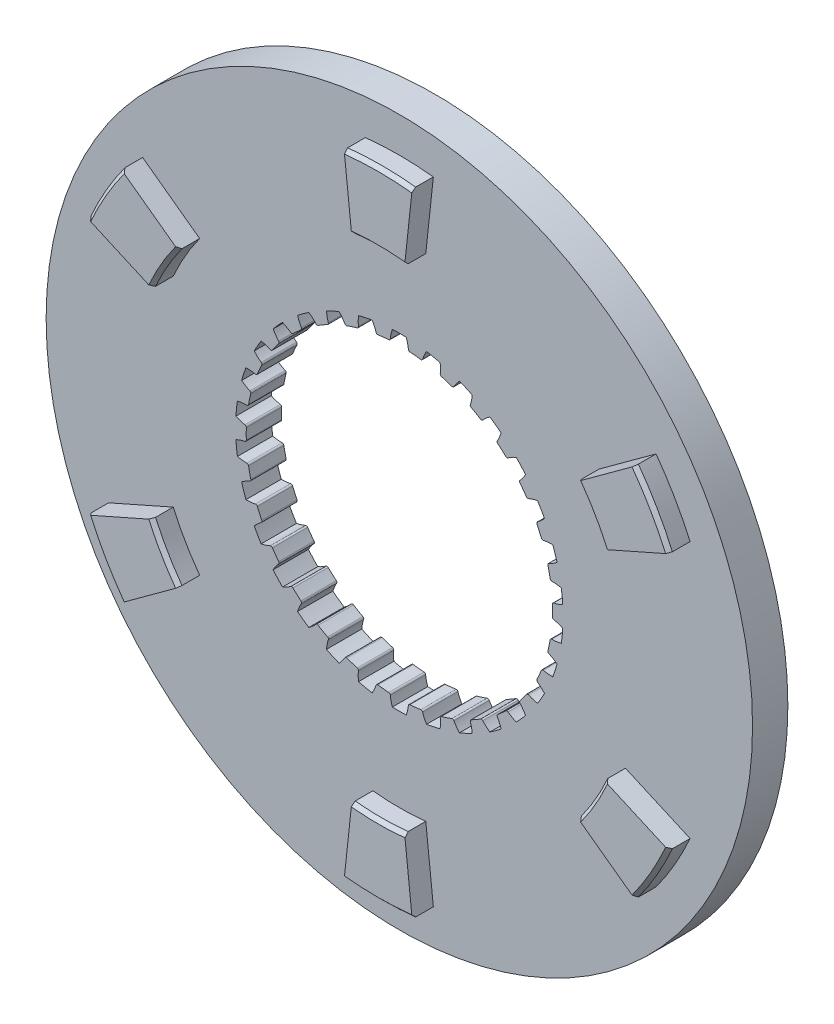
SolidWorks part; units mm, degrees
material "1.6587 (18CrNiMo7-6)"
ref_plane "Front Plane" through (0, 0, 0) normal (0, 0, 1) x (1, 0, 0)
ref_plane "Top Plane" through (0, 0, 0) normal (0, 1, 0) x (1, 0, 0)
ref_plane "Right Plane" through (0, 0, 0) normal (1, 0, 0) x (0, 0, -1)
sketch "Sketch1" plane through (0, 0, 0) normal (0, 0, 1) x (1, 0, 0)
  circle A1 centre (0, 0) radius 100
  dimension "D2" = 200
extrude "Boss-Extrude1" add sketch "Sketch1" along normal blind 10
sketch "Sketch2" plane through (0, 0, 10) normal (0, 0, 1) x (1, 0, 0)
  line L0 (0, 0) -> (10.2384, 95.1441)
  line L1 (0, 0) -> (-10.21, 94.8799)
  line L2 (0, 0) -> (0, 132.9785) construction
  line L3 (0, 0) -> (87.5164, 38.7053)
  line L4 (0, 0) -> (77.0634, 56.2821)
  line L5 (0, 0) -> (77.278, -56.4388)
  line L6 (0, 0) -> (87.2734, -38.5978)
  line L7 (0, 0) -> (-10.2384, -95.1441)
  line L8 (0, 0) -> (10.21, -94.8799)
  line L9 (0, 0) -> (-87.5164, -38.7053)
  line L10 (0, 0) -> (-77.0634, -56.2821)
  line L11 (0, 0) -> (-77.278, 56.4388)
  line L12 (0, 0) -> (-87.2734, 38.5978)
  circle A0 centre (0, 0) radius 70
  circle A1 centre (0, 0) radius 90
  point P19 (0, 0)
  dimension "D1" = 140
  dimension "D2" = 180
  dimension "D3" = 6
  dimension "D4" = 12.284
extrude "Boss-Extrude2" add sketch "Sketch2" along normal blind 6 contours L2 A0 L0 A1 | A0 L2 A1 L1 | L11 A1 L12 A0 | L9 A1 L10 A0 | L7 A1 L8 A0 | L5 A1 L6 A0 | L3 A1 L4 A0
chamfer "Chamfer1" distance 1 12 edges at (-77.9423, -45, 16) (-60.6218, -35, 16) (0, -70, 16) (0, -90, 16) (60.6218, -35, 16) (77.9423, -45, 16) (77.9423, 45, 16) (60.6218, 35, 16) (0, 70, 16) (0, 90, 16) (-77.9423, 45, 16) (-60.6218, 35, 16)
sketch "Sketch3" plane through (0, 0, 10) normal (0, 0, 1) x (1, 0, 0)
  line L0 (0, 0) -> (2.5692, 43.2738) construction
  line L1 (-9.3575, 42.328) -> (-12.2626, 41.5795) construction
  line L2 (0, 0) -> (-0.4299, 43.3479) construction
  line L3 (-0.4299, 43.3479) -> (2.5699, 43.3776) construction
  line L4 (0, 0) -> (-3.427, 43.2143) construction
  line L5 (-3.427, 43.2143) -> (2.5543, 43.6887) construction
  line L6 (0, 0) -> (-6.4076, 42.8738) construction
  line L7 (-6.4076, 42.8738) -> (2.4936, 44.2041) construction
  line L8 (0, 0) -> (-9.3575, 42.328) construction
  line L9 (-9.3575, 42.328) -> (2.3596, 44.9183) construction
  line L10 (2.5692, 43.2738) -> (-0.4299, 43.3479) construction
  line L11 (-0.4299, 43.3479) -> (-3.427, 43.2143) construction
  line L12 (-3.427, 43.2143) -> (-6.4076, 42.8738) construction
  line L13 (-6.4076, 42.8738) -> (-9.3575, 42.328) construction
  line L14 (0, 0) -> (-12.2626, 41.5795) construction
  line L15 (-12.2626, 41.5795) -> (2.1247, 45.8226) construction
  line L16 (0, 0) -> (-15.109, 40.6318) construction
  line L17 (-15.109, 40.6318) -> (1.7623, 46.9054) construction
  line L18 (-12.2626, 41.5795) -> (-15.109, 40.6318) construction
  line L19 (0, 0) -> (2.3551, 44.9383) construction
  line L20 (0, 0) -> (0, 54.7803) construction
  circle A0 centre (0, 0) radius 43.35
  circle A1 centre (0, 0) radius 45 construction
  circle A2 centre (0, 0) radius 46.35
  spline S0 degree 3 poles (2.5692, 43.2738) (2.5727, 43.4122) (2.544, 43.9656) (2.3322, 45.1974) (2.0036, 46.2564) (1.7623, 46.9054) knots 0 0 0 0 0.111137 0.444343 1 1 1 1
  spline S1 degree 3 poles (-2.5692, 43.2738) (-2.5727, 43.4122) (-2.544, 43.9656) (-2.3322, 45.1974) (-2.0036, 46.2564) (-1.7623, 46.9054) knots 0 0 0 0 0.111137 0.444343 1 1 1 1
  dimension "D1" = 86.7
  dimension "D2" = 90
  dimension "D3" = 92.7
  dimension "D4" = 3
  dimension "D5" = 3
  dimension "D6" = 6
  dimension "D7" = 9
  dimension "D8" = 12
  dimension "D9" = 15
  dimension "D10" = 18
  dimension "D11" = 3
extrude "Cut-Extrude2" cut sketch "Sketch3" against normal through all contours S1 A0 S0 A2
sketch "Sketch4" plane through (0, 0, 10) normal (0, 0, 1) x (1, 0, 0)
  circle A0 centre (0, 0) radius 43.35
  dimension "D1" = 86.7
extrude "Cut-Extrude3" cut sketch "Sketch4" against normal through all
fillet "Fillet2" radius 0.48 2 edges at (2.5692, 43.2738, 5) (-2.5692, 43.2738, 5)
pattern_circular "CirPattern3" count 30 over 360 about axis through (0, 0, 0) along (0, 0, 1) of "Cut-Extrude2", "Fillet2"
ref_plane "Plane1" through (0, 0, 5) normal (0, 0, 1) x (1, 0, 0)
mirror "Mirror1" about plane through (0, 0, 5) normal (0, 0, 1) of "Chamfer1", "Boss-Extrude2"
equation "\"val\"=3"
equation "\"D4@Sketch3\"=\"val\""
equation "\"D5@Sketch3\"=\"val\""
equation "\"D6@Sketch3\"=2*\"val\""
equation "\"D7@Sketch3\"=3*\"val\""
equation "\"D8@Sketch3\"=4*\"val\""
equation "\"D9@Sketch3\"=5*\"val\""
equation "\"D10@Sketch3\"=6*\"val\""
